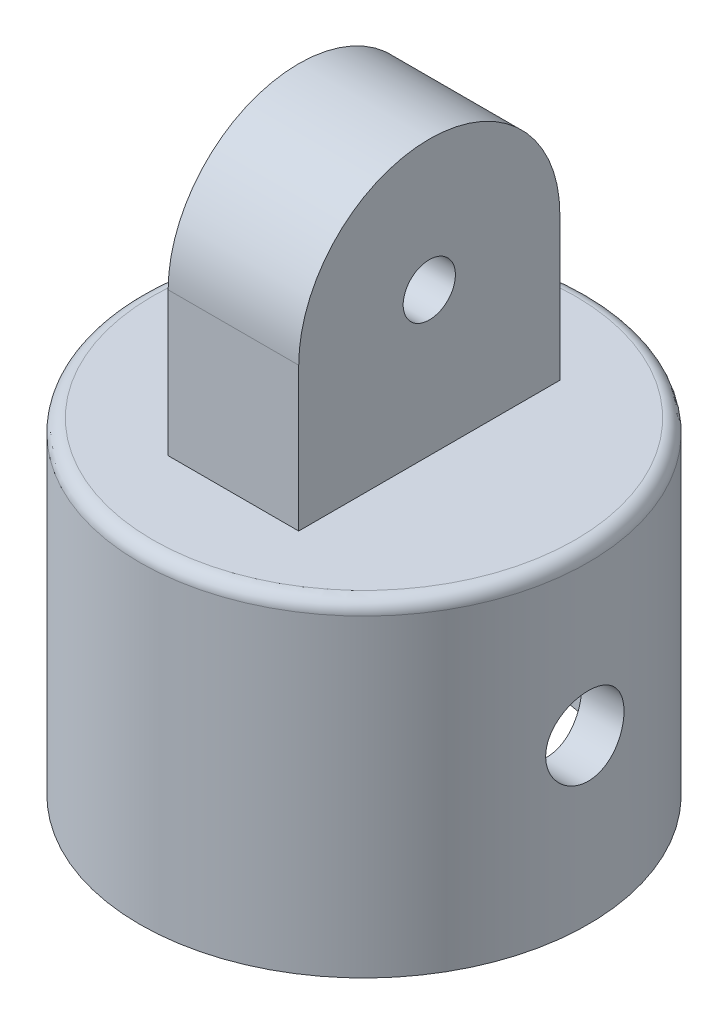
SolidWorks part; units mm, degrees
ref_plane "Front Plane" through (0, 0, 0) normal (0, 0, 1) x (1, 0, 0)
ref_plane "Top Plane" through (0, 0, 0) normal (0, 1, 0) x (1, 0, 0)
ref_plane "Right Plane" through (0, 0, 0) normal (1, 0, 0) x (0, 0, -1)
sketch "Sketch1" plane through (0, 0, 0) normal (0, 1, 0) x (1, 0, 0)
  circle A0 centre (0, 0) radius 12.5 construction
  circle A1 centre (0, 0) radius 17.175
  dimension "D1" = 34.35
extrude "Boss-Extrude2" add sketch "Sketch1" along normal blind 25
shell "Shell1" thickness 3.175
sketch "Sketch3" plane through (0, 0, 0) normal (1, 0, 0) x (0, 0, -1)
  line L0 (0, 0) -> (0, 25) construction
  line L1 (-17.175, 0) -> (17.175, 0) construction
  line L2 (17.175, 25) -> (-17.175, 25) construction
  circle A0 centre (0, 12.5) radius 3
  point P8 (0, 12.5)
  dimension "D1" = 6
extrude "Cut-Extrude1" cut sketch "Sketch3" against normal through all both and the other way through all
sketch "Sketch5" plane through (0, 0, 0) normal (1, 0, 0) x (0, 0, -1)
  line L3 (17.175, 25) -> (-17.175, 25) construction
  line L4 (-10, 36) -> (-10, 25)
  line L7 (10, 25) -> (10, 36)
  line L8 (-10, 25) -> (-10, 24.25)
  line L9 (-10, 24.25) -> (10, 24.25)
  line L10 (10, 25) -> (10, 24.25)
  circle A0 centre (0, 36) radius 2
  arc A1 (10, 36) -> (-10, 36) centre (0, 36) ccw
  dimension "D1" = 4
  dimension "D2" = 8
  dimension "D3" = 0.75
  dimension "D4" = 11
extrude "Boss-Extrude3" add sketch "Sketch5" along normal mid plane 10
fillet "Fillet1" radius 1 1 edges at (0, 25, 17.175)
equation "\"Dout 1\"= 35mm"
equation "\"thickness 1\"= 1.5mm"
equation "\"Bolt D 1\"= 8mm"
equation "\"keelOutDiameter\"= 1in"
equation "\"poleOutDiameter\"= 28mm"
equation "\"D1@Sketch1\"=\"poleOutDiameter\"+0.25in"
